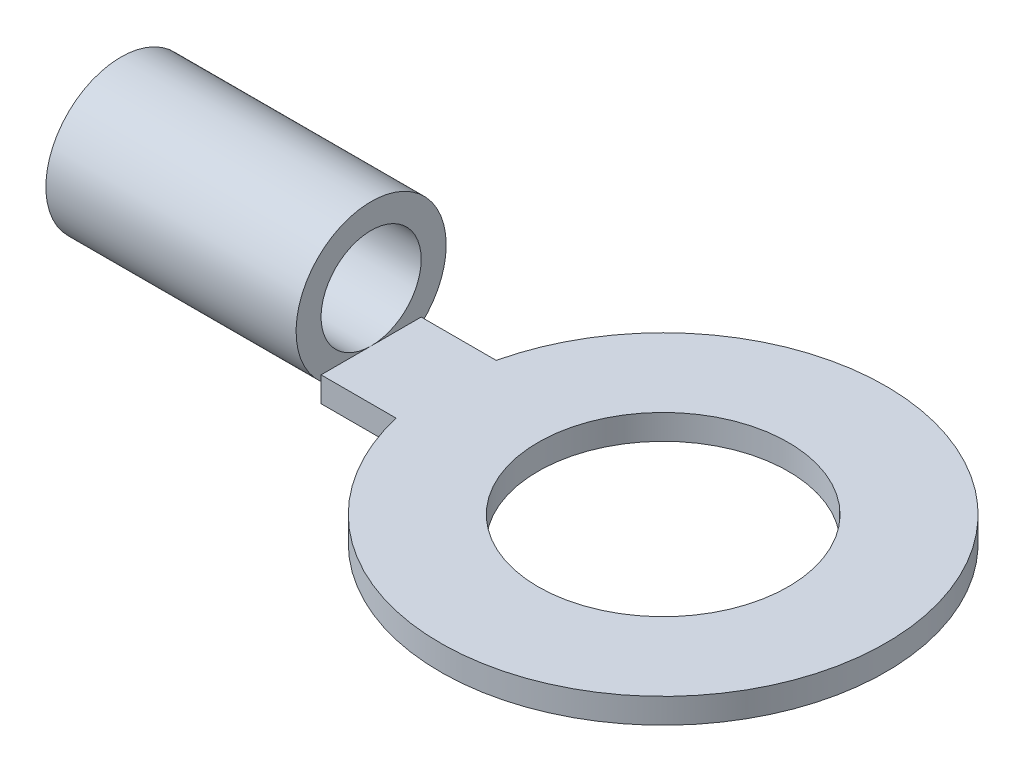
SolidWorks part; units mm, degrees
ref_plane "Front Plane" through (0, 0, 0) normal (0, 0, 1) x (1, 0, 0)
ref_plane "Top Plane" through (0, 0, 0) normal (0, 1, 0) x (1, 0, 0)
ref_plane "Right Plane" through (0, 0, 0) normal (1, 0, 0) x (0, 0, -1)
sketch "Sketch1" plane through (0, 0, 0) normal (0, 1, 0) x (1, 0, 0)
  line L0 (0, -1) -> (0, 1)
  line L1 (0, 1) -> (1.5, 1)
  line L2 (0, -1) -> (1.5, -1)
  arc A0 (1.5, -1) -> (1.5, 1) centre (5.8362, 0) ccw
  circle A1 centre (5.8362, 0) radius 2.5
  point P8 (0, 0)
  dimension "D1" = 5
  dimension "D2" = 8.9
  dimension "D3" = 1.5
  dimension "D4" = 2
extrude "Boss-Extrude1" add sketch "Sketch1" along normal blind 0.5
sketch "Sketch2" plane through (0, 0, 0) normal (1, 0, 0) x (0, 0, -1)
  circle A0 centre (0, 1.5) radius 1.5
  circle A1 centre (0, 1.5) radius 1
  dimension "D1" = 2
  dimension "D2" = 3
extrude "Boss-Extrude2" add sketch "Sketch2" against normal blind 5
